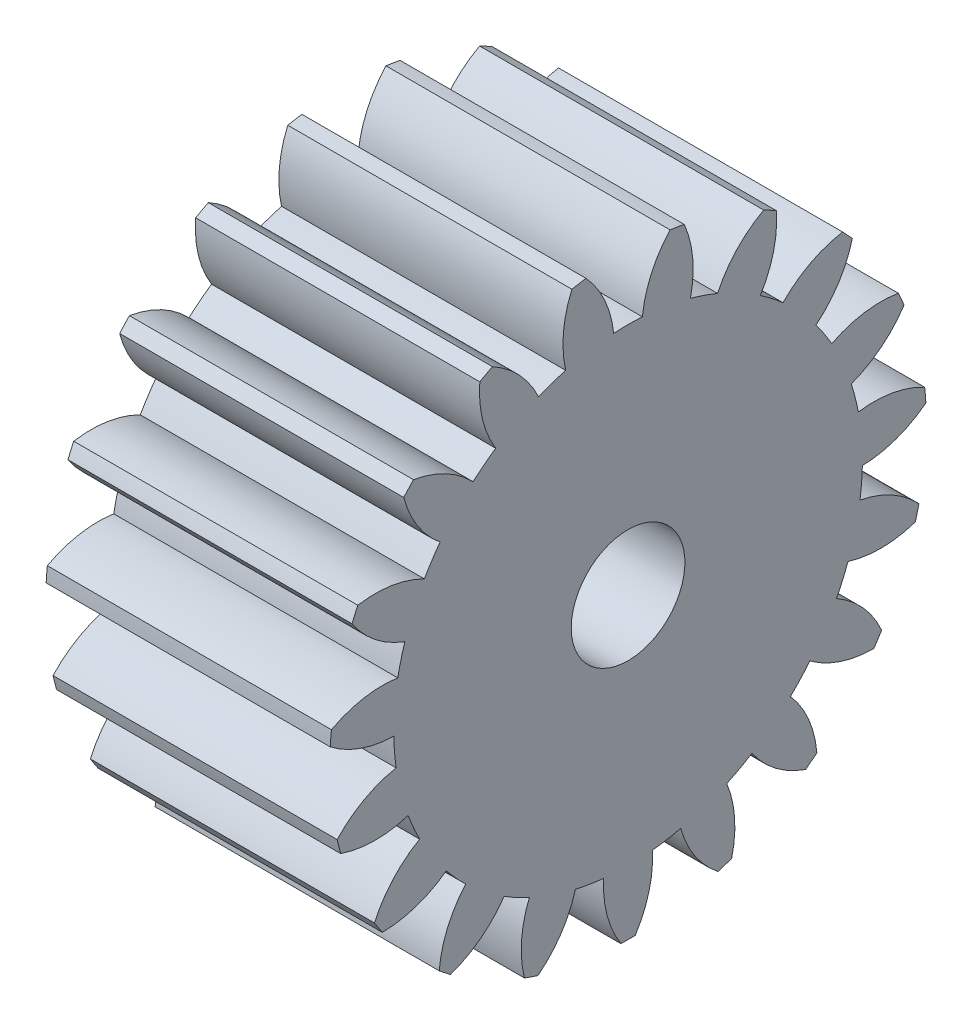
SolidWorks part; units mm, degrees
material "3.1325 (EN-AW 2017A)"
ref_plane "Plane1" through (0, 0, 0) normal (0, 0, 1) x (1, 0, 0)
ref_plane "Plane2" through (0, 0, 0) normal (0, 1, 0) x (1, 0, 0)
ref_plane "Plane3" through (0, 0, 0) normal (1, 0, 0) x (0, 0, -1)
sketch "HoldingSke" plane through (0, 0, 0) normal (0, 1, 0) x (1, 0, 0)
  line L0 (0, 0) -> (1.891, -0.6511)
  line L1 (-15, 0) -> (100, 0) construction
  line L2 (0, 0) -> (-2.1039, 2.3779)
  line L3 (0, 0) -> (-11.863, 4.5341)
  line L4 (0, 0) -> (8.1655, 2.8116)
  line L5 (0, 0) -> (-46.8476, -17.4728)
  line L6 (0, 0) -> (-4.1448, -2.7965)
  line L7 (-2.1039, 2.3779) -> (8.6586, 51.2059)
  line L8 (-76.2, 54.61) -> (-75.9, 54.61)
  line L9 (-71.009, 38.7566) -> (-53.1078, 45.2721)
  line L10 (-76.2, 71.12) -> (104.1128, 71.12)
  line L11 (0, 0) -> (-5, 0)
  line L12 (-76.2, 101.6) -> (-76.181, 101.6)
  line L13 (24.9733, 27.94) -> (52.9518, 28.4284)
  line L14 (24.9733, 27.94) -> (24.9743, 27.94)
  line L15 (24.9733, 27.94) -> (100.4006, 29.5858)
  line L16 (-63.627, -0.5) -> (-12.827, -0.5)
  circle A0 centre (0, 0) radius 1
  circle A1 centre (0, 0) radius 4.124
  circle A2 centre (0, 0) radius 37.5
  circle A3 centre (0, 0) radius 1
  dimension "MHD" = 8.248
  dimension "Hub_dia" = 75
  dimension "Bore" = 2
  dimension "MBD" = 2
  dimension "Num_teeth" = 19
  dimension "Pitch_radius" = 180.3128
  dimension "Pitch" = 2
  dimension "Width" = 5
  dimension "Overall_len" = 50
  dimension "Show_teeth" = 19
  dimension "Thickness" = 5
  dimension "OAL" = 50.0001
  dimension "T_dim" = 0.3
  dimension "Ap" = 20
  dimension "H" = 19.05
  dimension "Backlash" = 0.019
  dimension "Addendum_fac" = 1
  dimension "Dedendum_fac" = 1.25
  dimension "Clearance_fac" = 0.25
  dimension "Dedendum_add" = 0.001
  dimension "Module" = 0.5
sketch "BasProSke" plane through (0, 0, 0) normal (0, 1, 0) x (1, 0, 0)
  line L0 (-10, 0) -> (60, 0) construction
  line L1 (0, 0) -> (0, 5.25)
  line L2 (0, 0) -> (5, 0)
  line L3 (5, 0) -> (5, 5.25)
  line L4 (5, 5.25) -> (0, 5.25)
  dimension "Diameter" = 10.5
  dimension "Thickness" = 5
revolve "Base-Revolve" add sketch "BasProSke" angle 360 about L0
sketch "TooCutSke" plane through (0, 0, 0) normal (1, 0, 0) x (0, 0, -1)
  line L1 (0, 0) -> (0, 107) construction
  line L2 (0, 0) -> (-0.4255, 4.7309) construction
  line L3 (0, 0) -> (-1.5592, 9.3436) construction
  line L4 (-0.4255, 4.7309) -> (-0.7796, 4.6718) construction
  arc A0 (0.2525, 4.1163) -> (-0.2525, 4.1163) centre (0, 0) ccw
  arc A1 (0.7603, 5.2203) -> (-0.7603, 5.2203) centre (0, 0) ccw
  circle A2 centre (0, 0) radius 4.75 construction
  circle A3 centre (0, 0) radius 4.4635 construction
  arc A4 (-0.2525, 4.1163) -> (-0.7603, 5.2203) centre (-2.1419, 3.9161) ccw
  arc A5 (0.7603, 5.2203) -> (0.2525, 4.1163) centre (2.1419, 3.9161) ccw
  dimension "Root_dia" = 8.248
  dimension "Overcut_dia" = 10.5508
  dimension "Pitch_dia" = 9.5
  dimension "Base_dia" = 8.9271
  dimension "Flank_rad" = 1.9
  dimension "Half_ang" = 9.474
  dimension "Half_CT" = 0.359
extrude "ToothCut" cut sketch "TooCutSke" along normal through all
fillet "Breaks" [suppressed] radius 0.01
fillet "RootFillets" [suppressed] radius 0.126
pattern_circular "TeethCuts" count 19 every 18.947 about axis through (-10, 0, 0) along (1, 0, 0) of "ToothCut", "RootFillets", "Breaks"
sketch "HubNeaOneSke" plane through (0, 0, 0) normal (-1, 0, 0) x (0, 0, 1)
  circle A0 centre (0, 0) radius 4.124
  dimension "Diameter" = 8.248
extrude "HubNearOne" [suppressed] add sketch "HubNeaOneSke" along normal blind 45.0001
sketch "HubNeaBotSke" plane through (0, 0, 0) normal (-1, 0, 0) x (0, 0, 1)
  circle A0 centre (0, 0) radius 4.124
  dimension "Diameter" = 8.248
extrude "HubNearBoth" [suppressed] add sketch "HubNeaBotSke" along normal blind 22.5
ref_plane "FarPln" through (5, 0, 0) normal (1, 0, 0) x (0, 0, -1)
sketch "HubFarSke" plane through (5, 0, 0) normal (1, 0, 0) x (0, 0, -1)
  circle A0 centre (0, 0) radius 4.124
  dimension "Diameter" = 8.248
extrude "HubFar" [suppressed] add sketch "HubFarSke" along normal blind 22.5
sketch "BorSke" plane through (0, 0, 0) normal (1, 0, 0) x (0, 0, -1)
  circle A0 centre (0, 0) radius 1
  dimension "Diameter" = 2
extrude "Bore" cut sketch "BorSke" along normal mid plane 100.0001
sketch "KeySke" plane through (0, 0, 0) normal (1, 0, 0) x (0, 0, -1)
  line L0 (-0.4, 0) -> (-0.4, 1.3)
  line L1 (-0.4, 1.3) -> (0.4, 1.3)
  line L2 (0.4, 1.3) -> (0.4, 0)
  line L3 (0, 0) -> (0, 34) construction
  line L4 (-0.4, 0) -> (0.4, 0)
  dimension "Offset" = 1.3
  dimension "Width" = 0.8
extrude "Keyway" [suppressed] cut sketch "KeySke" along normal mid plane 100.0001
pattern_circular "Keyway2" [suppressed] count 2 every 90 about axis through (-10, 0, 0) along (1, 0, 0)
equation "' \"Module@HoldingSke\" = 6.35"
equation "' \"Num_teeth@HoldingSke\" = 12"
equation "' \"Ap@HoldingSke\" =  20"
equation "' \"Width@HoldingSke\" = 0.5 * 25.4"
equation "' \"Hub_dia@HoldingSke\"= 1 * 25.4"
equation "' \"Overall_len@HoldingSke\" = 1.0 * 25.4"
equation "' \"Bore@HoldingSke\" = 0.75 * 25.4"
equation "' \"T_dim@HoldingSke\" = 0.1 * 25.4"
equation "' \"Width@KeySke\" = 0.25 * 25.4"
equation "' \"Show_teeth@HoldingSke\" = 13"
equation "' \"Backlash@HoldingSke\" = 0.009 * 25.4"
equation "' \"Addendum_fac@HoldingSke\" = 1.0"
equation "' \"Dedendum_fac@HoldingSke\" = 1.25"
equation "' \"Dedendum_add@HoldingSke\" = 0.00005 * 25.4"
equation "' \"Clearance_fac@HoldingSke\" = 0.25"
equation "\"Pitch@HoldingSke\" = 1 / \"Module@HoldingSke\""
equation "\"Overcut_dia@TooCutSke\" = (\"Num_teeth@HoldingSke\" + 2 * \"Addendum_fac@HoldingSke\") / \"Pitch@HoldingSke\" + 0.002 * 25.4"
equation "\"Pitch_dia@TooCutSke\" = \"Num_teeth@HoldingSke\" / \"Pitch@HoldingSke\""
equation "\"Base_dia@TooCutSke\" = \"Num_teeth@HoldingSke\" / \"Pitch@HoldingSke\" * cos((\"Ap@HoldingSke\"  * 3.14159265 / 180))"
equation "\"Root_dia@TooCutSke\" = (\"Num_teeth@HoldingSke\" + 2) / \"Pitch@HoldingSke\" - 2 * (\"Addendum_fac@HoldingSke\" + \"Dedendum_fac@HoldingSke\") / \"Pitch@HoldingSke\" - \"Dedendum_add@HoldingSke\" * 2"
equation "\"Half_ang@TooCutSke\" = 180 / \"Num_teeth@HoldingSke\""
equation "\"Half_CT@TooCutSke\" = \"Num_teeth@HoldingSke\" / \"Pitch@HoldingSke\" * sin((3.14159265 / 2 / \"Num_teeth@HoldingSke\")) / 2 - 7 * \"Backlash@HoldingSke\" / 4"
equation "\"Flank_rad@TooCutSke\" = \"Num_teeth@HoldingSke\" / \"Pitch@HoldingSke\" / 5"
equation "\"Radius@RootFillets\" = \"Clearance_fac@HoldingSke\" / \"Pitch@HoldingSke\" + \"Dedendum_add@HoldingSke\""
equation "\"Break_rad@Breaks\" = 0.02 / \"Pitch@HoldingSke\""
equation "\"Thickness@HoldingSke\" = \"Width@HoldingSke\""
equation "\"OAL@HoldingSke\" = \"Thickness@HoldingSke\""
equation "\"MHD@HoldingSke\" = (\"Num_teeth@HoldingSke\" + 2) / \"Pitch@HoldingSke\" - 2 * (\"Addendum_fac@HoldingSke\" + \"Dedendum_fac@HoldingSke\")  / \"Pitch@HoldingSke\" - \"Dedendum_add@HoldingSke\" * 2"
equation "\"MBD@HoldingSke\" = (\"Num_teeth@HoldingSke\" + 2) / \"Pitch@HoldingSke\" - 2 * (\"Addendum_fac@HoldingSke\" + \"Dedendum_fac@HoldingSke\")  / \"Pitch@HoldingSke\" - \"Dedendum_add@HoldingSke\" * 2 - 0.002 * 25.4"
equation "\"MHD@HoldingSke\" = ((sgn( \"MHD@HoldingSke\" - \"Hub_dia@HoldingSke\" )-1)*( \"MHD@HoldingSke\" - \"Hub_dia@HoldingSke\" ))/-2+ \"Hub_dia@HoldingSke\""
equation "\"MBD@HoldingSke\" = ((sgn( \"MBD@HoldingSke\" - \"Bore@HoldingSke\" )-1)*( \"MBD@HoldingSke\" - \"Bore@HoldingSke\" ))/-2+ \"Bore@HoldingSke\""
equation "\"OAL@HoldingSke\" = ((sgn( \"OAL@HoldingSke\" - \"Overall_len@HoldingSke\" )+1)*( \"OAL@HoldingSke\" - \"Overall_len@HoldingSke\" ))/2 + \"Overall_len@HoldingSke\" + 0.000002 * 25.4"
equation "\"Num_teeth@TeethCuts\" = int( \"Show_teeth@HoldingSke\" ) + 1"
equation "\"Num_teeth@TeethCuts\" = ((sgn( \"Num_teeth@TeethCuts\" - \"Num_teeth@HoldingSke\" )-1)*( \"Num_teeth@TeethCuts\" - \"Num_teeth@HoldingSke\" ))/-2+ \"Num_teeth@HoldingSke\""
equation "\"Num_teeth@TeethCuts\" = ((sgn( \"Num_teeth@TeethCuts\" - 2.0)+1)*( \"Num_teeth@TeethCuts\" - 2.0))/2 +2.0"
equation "\"Angle@TeethCuts\" = 360.0 / \"Num_teeth@HoldingSke\""
equation "\"Diameter@BasProSke\" = (\"Num_teeth@HoldingSke\" + 2 * \"Addendum_fac@HoldingSke\") / \"Pitch@HoldingSke\""
equation "\"Thickness@BasProSke\"  = \"Thickness@HoldingSke\""
equation "' \"Fillet_rad@BasProSke\" =  \"Thickness@HoldingSke\" * 0.05"
equation "\"MHD@HoldingSke\" = ((sgn( \"MHD@HoldingSke\" - \"Root_dia@TooCutSke\" )-1)*( \"MHD@HoldingSke\" - \"Root_dia@TooCutSke\" ))/-2+ \"Root_dia@TooCutSke\""
equation "\"Diameter@HubNeaOneSke\" = \"MHD@HoldingSke\""
equation "\"Length@HubNearOne\" = \"OAL@HoldingSke\" - \"Thickness@BasProSke\""
equation "\"Diameter@HubNeaBotSke\" = \"MHD@HoldingSke\""
equation "\"Length@HubNearBoth\" = ( \"OAL@HoldingSke\" - \"Thickness@BasProSke\" ) / 2.0"
equation "\"Thickness@FarPln\" = \"Thickness@BasProSke\""
equation "\"Diameter@HubFarSke\" = \"MHD@HoldingSke\""
equation "\"Length@HubFar\" = ( \"OAL@HoldingSke\" - \"Thickness@BasProSke\" ) / 2.0"
equation "\"Diameter@BorSke\" = \"MBD@HoldingSke\""
equation "\"D1@Bore\" = \"OAL@HoldingSke\" * 2.0"
equation "\"D1@Keyway\" = \"OAL@HoldingSke\" * 2.0"
equation "\"Offset@KeySke\" = \"T_dim@HoldingSke\" + \"MBD@HoldingSke\" / 2.0"
